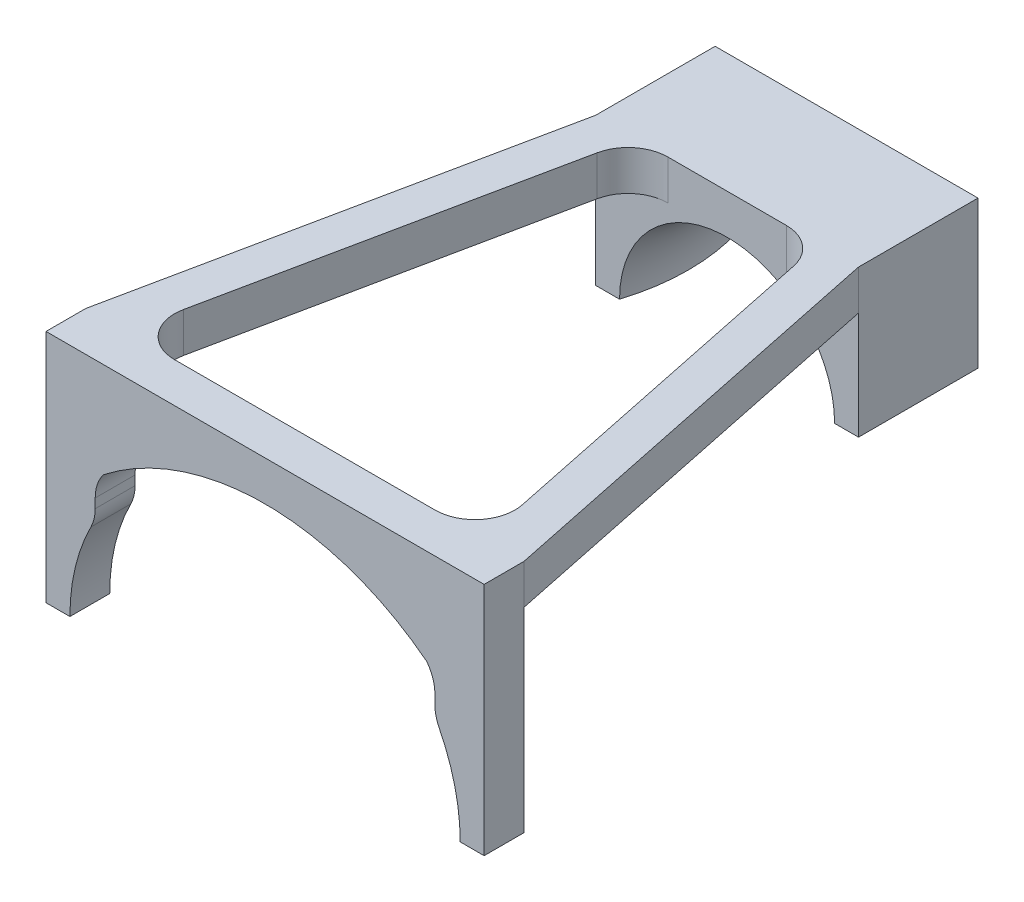
SolidWorks part; units mm, degrees
ref_plane "Front Plane" through (0, 0, 0) normal (0, 0, 1) x (1, 0, 0)
ref_plane "Top Plane" through (0, 0, 0) normal (0, 1, 0) x (1, 0, 0)
ref_plane "Right Plane" through (0, 0, 0) normal (1, 0, 0) x (0, 0, -1)
sketch "Sketch1" plane through (0, 0, 0) normal (0, 0, 1) x (1, 0, 0)
  line L1 (0, 0) -> (-38.2853, 0) construction
  line L2 (0, 0) -> (0, 65.2519) construction
  line L4 (-21, 16.3042) -> (-19.2879, 14.282) construction
  line L8 (-21.3231, 14.4853) -> (-21.3231, 13.3171)
  line L19 (21.3231, 14.4853) -> (21.3231, 13.3171)
  line L20 (-24.5, 0) -> (-27.5, 0)
  line L21 (-27.5, 0) -> (-27.5, 29.5)
  line L22 (-27.5, 29.5) -> (27.5, 29.5)
  line L23 (27.5, 0) -> (27.5, 29.5)
  line L24 (24.5, 0) -> (27.5, 0)
  arc A9 (0, 24.5) -> (-20.2968, 17.52) centre (0, -8.5) ccw
  arc A10 (0, 24.5) -> (-21.3231, 16.6858) centre (0, -8.5) ccw construction
  arc A24 (21.8615, 11.06) -> (24.5, 0) centre (0, 0) cw
  arc A25 (-21.3231, 13.3171) -> (-21.8615, 11.06) centre (-26.3231, 13.3171) cw
  arc A26 (-20.2968, 17.52) -> (-21.3231, 14.4853) centre (-16.3231, 14.4853) ccw
  arc A28 (0, 24) -> (-21, 16.3042) centre (0, -8.5) ccw construction
  arc A30 (0, 24) -> (-24, 0) centre (0, 0) ccw construction
  arc A31 (-21.8615, 11.06) -> (-24.5, 0) centre (0, 0) ccw
  arc A32 (21.3231, 13.3171) -> (21.8615, 11.06) centre (26.3231, 13.3171) ccw
  arc A33 (20.2968, 17.52) -> (21.3231, 14.4853) centre (16.3231, 14.4853) cw
  arc A35 (0, 24.5) -> (20.2968, 17.52) centre (0, -8.5) cw
  point P4 (0, 24)
  point P5 (0, 24)
  point P12 (0, 29.5)
  dimension "D1" = 3
  dimension "D2" = 65
  dimension "D7" = 48
  dimension "D4" = 5
  dimension "D5" = 0.5
  dimension "D3" = 21
extrude "Boss-Extrude1" add sketch "Sketch1" along normal blind 5
sketch "Sketch2" plane through (0, 0, 0) normal (0, 0, 1) x (1, 0, 0)
  line L1 (-16.5, 11) -> (-13.5, 11)
  line L3 (-16.5, 11) -> (-16.5, 29.5)
  line L4 (27.5, 29.5) -> (-27.5, 29.5) construction
  line L7 (40.4426, 0) -> (0, 0) construction
  line L8 (0, 0) -> (0, 39.2883) construction
  line L9 (-16.5, 29.5) -> (16.5, 29.5)
  line L10 (16.5, 11) -> (13.5, 11)
  line L11 (16.5, 11) -> (16.5, 29.5)
  arc A0 (13.5, 11) -> (-13.5, 11) centre (0, 11) ccw
  point P12 (0, 29.5)
  dimension "D1" = 27
  dimension "D2" = 3
  dimension "D3" = 11
extrude "Boss-Extrude2" add sketch "Sketch2" against normal blind 15 from offset 53 separate body offset against normal yes
sketch "Sketch5" plane through (0, 11, 0) normal (0, -1, 0) x (1, 0, 0)
  line L1 (13.5, -68) -> (13.5, -53) construction
  line L2 (13.5, -86.2178) -> (13.5, -60.5) construction
  line L3 (13.5, -60.5) -> (-13.5, -60.5) construction
  line L7 (-13.5, -68) -> (-13.5, -53) construction
  line L8 (0, -60.5) -> (0, -94.9594) construction
  line L9 (13.5, -53) -> (13.5, -68)
  arc A1 (13.5, -53) -> (13.5, -68) centre (37.3485, -60.5) ccw
  dimension "D1" = 50
revolve "Revolve2" add sketch "Sketch5" angle 180 about L8
sketch "Sketch6" plane through (0, 29.5, 0) normal (0, 1, 0) x (1, 0, 0)
  line L0 (-27.5, 0) -> (-16.5, 53)
  line L1 (0, -13.5751) -> (0, 94.3369) construction
  line L2 (-27.5, 0) -> (-22.5, 0)
  line L3 (27.5, 0) -> (-27.5, 0) construction
  line L4 (-22.5, 0) -> (-11.5, 53)
  line L5 (16.5, 53) -> (-16.5, 53) construction
  line L6 (-11.5, 53) -> (-16.5, 53)
  line L7 (22.5, 0) -> (11.5, 53)
  line L8 (27.5, 0) -> (22.5, 0)
  line L9 (27.5, 0) -> (16.5, 53)
  line L10 (11.5, 53) -> (16.5, 53)
  dimension "D1" = 5
extrude "Boss-Extrude3" add sketch "Sketch6" against normal blind 5
fillet "Fillet1" radius 5 4 edges at (-11.5, 27, -53) (11.5, 27, -53) (-22.5, 27, 0) (22.5, 27, 0)
